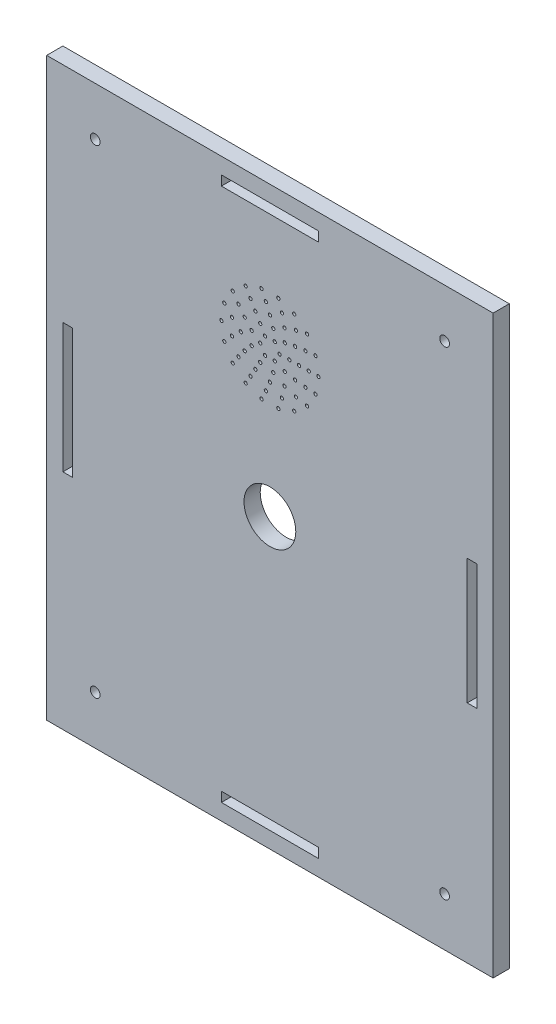
SolidWorks part; units mm, degrees
ref_plane "Front Plane" through (0, 0, 0) normal (0, 0, 1) x (1, 0, 0)
ref_plane "Top Plane" through (0, 0, 0) normal (0, 1, 0) x (1, 0, 0)
ref_plane "Right Plane" through (0, 0, 0) normal (1, 0, 0) x (0, 0, -1)
sketch "Sketch2" plane through (0, 0, 0) normal (0, 0, 1) x (1, 0, 0)
  line L1 (69, -89) -> (-69, -89)
  line L2 (69, -89) -> (69, 89)
  line L3 (69, 89) -> (-69, 89)
  line L4 (-69, -89) -> (-69, 89)
  line L5 (69, -89) -> (-69, 89) construction
  line L6 (69, 89) -> (-69, -89) construction
  point P0 (0, 0)
  dimension "D1" = 178
  dimension "D2" = 138
extrude "Boss-Extrude1" add sketch "Sketch2" along normal blind 5
sketch "Sketch3" plane through (0, 0, 5) normal (0, 0, 1) x (1, 0, 0)
  line L1 (-15, 84) -> (15, 84)
  line L2 (-15, 84) -> (-15, 81)
  line L3 (-15, 81) -> (15, 81)
  line L4 (15, 84) -> (15, 81)
  line L5 (-15, 84) -> (15, 81) construction
  line L6 (-15, 81) -> (15, 84) construction
  line L11 (69, 89) -> (-69, 89) construction
  point P0 (0, 82.5)
  point P8 (0, 89)
  point P10 (0, 84)
  dimension "D1" = 0
  dimension "D2" = 5
  dimension "D3" = 3
extrude "Cut-Extrude1" cut sketch "Sketch3" against normal through all
sketch "Sketch4" plane through (0, 0, 5) normal (0, 0, 1) x (1, 0, 0)
  line L1 (-15, -81) -> (15, -81)
  line L2 (-15, -81) -> (-15, -84)
  line L3 (-15, -84) -> (15, -84)
  line L4 (15, -81) -> (15, -84)
  line L5 (-15, -81) -> (15, -84) construction
  line L6 (-15, -84) -> (15, -81) construction
  line L8 (-69, -89) -> (69, -89) construction
  point P0 (0, -82.5)
  point P7 (0, -89)
  point P8 (0, -84)
  dimension "D1" = 0
  dimension "D2" = 3
  dimension "D3" = 5
sketch "Sketch5" plane through (0, 0, 5) normal (0, 0, 1) x (1, 0, 0)
  line L1 (-64, 20) -> (-61, 20)
  line L2 (-64, 20) -> (-64, -20)
  line L3 (-64, -20) -> (-61, -20)
  line L4 (-61, 20) -> (-61, -20)
  line L5 (-64, 20) -> (-61, -20) construction
  line L6 (-64, -20) -> (-61, 20) construction
  line L7 (-69, 89) -> (-69, -89) construction
  point P0 (-62.5, 0)
  point P7 (-69, 0)
  point P8 (-64, 0)
  dimension "D1" = 0
  dimension "D2" = 3
  dimension "D3" = 5
sketch "Sketch6" plane through (0, 0, 5) normal (0, 0, 1) x (1, 0, 0)
  line L1 (61, 19.3548) -> (64, 19.3548)
  line L2 (61, 19.3548) -> (61, -19.3548)
  line L3 (61, -19.3548) -> (64, -19.3548)
  line L4 (64, 19.3548) -> (64, -19.3548)
  line L5 (61, 19.3548) -> (64, -19.3548) construction
  line L6 (61, -19.3548) -> (64, 19.3548) construction
  line L8 (-69, -89) -> (69, -89) construction
  line L10 (69, -89) -> (69, 89) construction
  point P0 (64, 0)
  point P6 (62.5, 0)
  dimension "D1" = 89
  dimension "D2" = 5
  dimension "D3" = 3
extrude "Cut-Extrude2" cut sketch "Sketch4" against normal blind 8
extrude "Cut-Extrude3" cut sketch "Sketch6" against normal blind 8
extrude "Cut-Extrude4" cut sketch "Sketch5" against normal blind 8
sketch "Sketch8" plane through (0, 0, 5) normal (0, 0, 1) x (1, 0, 0)
  line L0 (69, 89) -> (-69, 89) construction
  line L2 (69, -89) -> (69, 89) construction
  line L6 (-69, 89) -> (-69, -89) construction
  line L8 (-69, -89) -> (69, -89) construction
  line L11 (69, 89) -> (-69, 89) construction
  circle A0 centre (54, -74) radius 1.5
  circle A1 centre (54, 74) radius 1.5
  circle A2 centre (-54, 74) radius 1.5
  circle A3 centre (-54, -74) radius 1.5
  dimension "D1" = 3
  dimension "D4" = 3
  dimension "D6" = 3
  dimension "D10" = 15
  dimension "D2" = 15
  dimension "D3" = 2
  dimension "D5" = 15
  dimension "D7" = 15
  dimension "D8" = 15
  dimension "D9" = 15
  dimension "D11" = 15
  dimension "D12" = 15
extrude "Cut-Extrude5" cut sketch "Sketch8" against normal through all
sketch "Sketch10" plane through (0, 0, 0) normal (0, 0, -1) x (-1, 0, 0)
  circle A0 centre (0, 0) radius 8
  dimension "D1" = 0
  dimension "D2" = 16
extrude "Cut-Extrude8" cut sketch "Sketch10" against normal blind 10 contours A0
sketch "Sketch11" plane through (0, 0, 0) normal (0, 0, -1) x (-1, 0, 0)
  circle A0 centre (0, 45) radius 15 construction
  circle A1 centre (-3, 45) radius 0.5
  circle A2 centre (-1.5, 47.5981) radius 0.5
  circle A3 centre (1.5, 47.5981) radius 0.5
  circle A4 centre (3, 45) radius 0.5
  circle A5 centre (1.5, 42.4019) radius 0.5
  circle A6 centre (-1.5, 42.4019) radius 0.5
  circle A7 centre (-6, 45) radius 0.5
  circle A8 centre (-9, 45) radius 0.5
  circle A9 centre (-12, 45) radius 0.5
  circle A10 centre (-15, 45) radius 0.5
  circle A11 centre (-4.5963, 48.8567) radius 0.5
  circle A12 centre (-1.0419, 50.9088) radius 0.5
  circle A13 centre (3, 50.1962) radius 0.5
  circle A14 centre (5.6382, 47.0521) radius 0.5
  circle A15 centre (5.6382, 42.9479) radius 0.5
  circle A16 centre (3, 39.8038) radius 0.5
  circle A17 centre (-1.0419, 39.0912) radius 0.5
  circle A18 centre (-4.5963, 41.1433) radius 0.5
  circle A19 centre (-7.7942, 49.5) radius 0.5
  circle A20 centre (-4.5, 52.7942) radius 0.5
  circle A21 centre (0, 54) radius 0.5
  circle A22 centre (4.5, 52.7942) radius 0.5
  circle A23 centre (7.7942, 49.5) radius 0.5
  circle A24 centre (9, 45) radius 0.5
  circle A25 centre (7.7942, 40.5) radius 0.5
  circle A26 centre (4.5, 37.2058) radius 0.5
  circle A27 centre (0, 36) radius 0.5
  circle A28 centre (-4.5, 37.2058) radius 0.5
  circle A29 centre (-10.9625, 49.8808) radius 0.5
  circle A30 centre (-8.0296, 53.9177) radius 0.5
  circle A31 centre (-3.7082, 56.4127) radius 0.5
  circle A32 centre (1.2543, 56.9343) radius 0.5
  circle A33 centre (6, 55.3923) radius 0.5
  circle A34 centre (9.7082, 52.0534) radius 0.5
  circle A35 centre (11.7378, 47.4949) radius 0.5
  circle A36 centre (11.7378, 42.5051) radius 0.5
  circle A37 centre (9.7082, 37.9466) radius 0.5
  circle A38 centre (6, 34.6077) radius 0.5
  circle A39 centre (1.2543, 33.0657) radius 0.5
  circle A40 centre (-3.7082, 33.5873) radius 0.5
  circle A41 centre (-14.0954, 50.1303) radius 0.5
  circle A42 centre (-11.4907, 54.6418) radius 0.5
  circle A43 centre (-7.5, 57.9904) radius 0.5
  circle A44 centre (-2.6047, 59.7721) radius 0.5
  circle A45 centre (2.6047, 59.7721) radius 0.5
  circle A46 centre (7.5, 57.9904) radius 0.5
  circle A47 centre (11.4907, 54.6418) radius 0.5
  circle A48 centre (14.0954, 50.1303) radius 0.5
  circle A49 centre (15, 45) radius 0.5
  circle A50 centre (14.0954, 39.8697) radius 0.5
  circle A51 centre (11.4907, 35.3582) radius 0.5
  circle A52 centre (7.5, 32.0096) radius 0.5
  circle A53 centre (-7.7942, 40.5) radius 0.5
  circle A54 centre (-8.0296, 36.0823) radius 0.5
  circle A55 centre (-10.9625, 40.1192) radius 0.5
  circle A56 centre (2.6047, 30.2279) radius 0.5
  circle A57 centre (-2.6047, 30.2279) radius 0.5
  circle A58 centre (-7.5, 32.0096) radius 0.5
  circle A59 centre (-11.4907, 35.3582) radius 0.5
  circle A60 centre (-14.0954, 39.8697) radius 0.5
  point P17 (0, 45)
  point P42 (0, 45)
  point P63 (0, 45)
  point P88 (0, 45)
  point P113 (0, 45)
  dimension "D1" = 30
  dimension "D3" = 1
  dimension "D2" = 45
  dimension "D4" = 3
  dimension "D6" = 5
  dimension "D5" = 6
  dimension "D7" = 9
  dimension "D8" = 12
  dimension "D9" = 15
  dimension "D10" = 18
extrude "Cut-Extrude10" cut sketch "Sketch11" against normal blind 10
